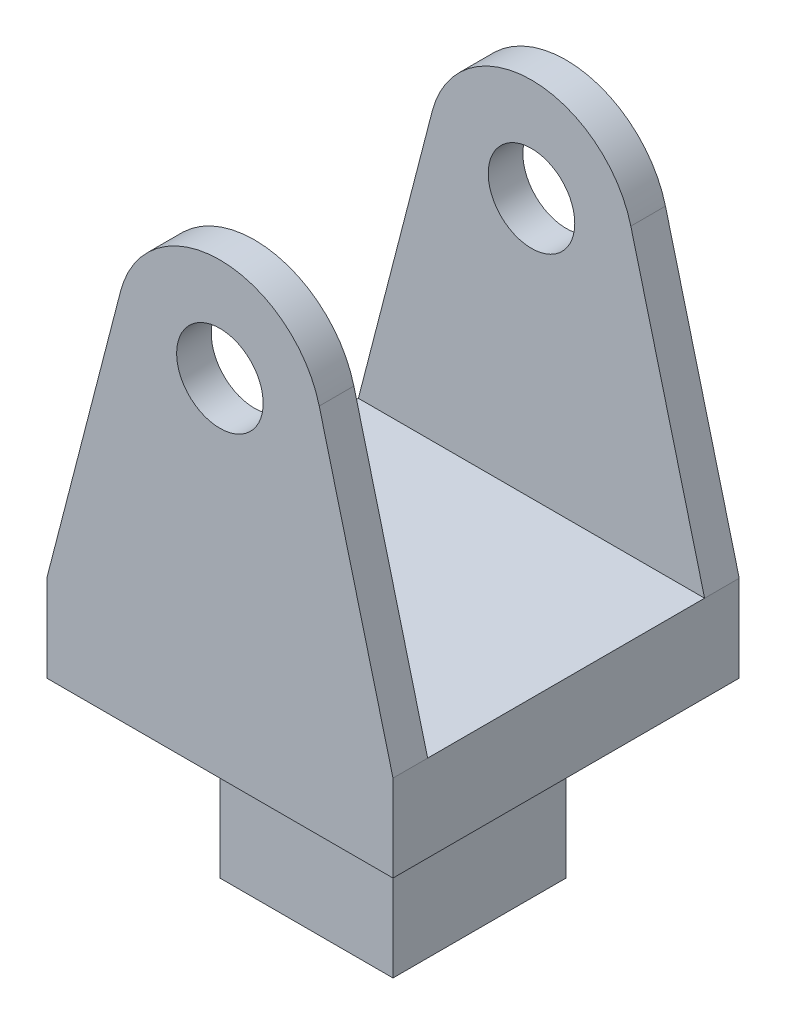
SolidWorks part; units mm, degrees
ref_plane "Front Plane" through (0, 0, 0) normal (0, 0, 1) x (1, 0, 0)
ref_plane "Top Plane" through (0, 0, 0) normal (0, 1, 0) x (1, 0, 0)
ref_plane "Right Plane" through (0, 0, 0) normal (1, 0, 0) x (0, 0, -1)
sketch "Sketch3" plane through (0, 0, 0) normal (0, 1, 0) x (1, 0, 0)
  line L1 (10, 10) -> (-10, 10)
  line L2 (-10, 10) -> (-10, -10)
  line L3 (-10, -10) -> (10, -10)
  line L4 (10, -10) -> (10, 10)
  circle A0 centre (0, 0) radius 10 construction
  dimension "D1" = 20
extrude "Boss-Extrude1" add sketch "Sketch3" along normal blind 30
sketch "Sketch4" plane through (-10, 0, 0) normal (-1, 0, 0) x (0, 0, 1)
  line L0 (-10, 30) -> (10, 30) construction
  line L1 (-8, 30) -> (8, 30)
  line L2 (-8, 30) -> (-8, 5)
  line L3 (-8, 5) -> (8, 5)
  line L4 (8, 30) -> (8, 5)
  line L5 (-10, 0) -> (10, 0) construction
  line L6 (0, 0) -> (0, 28.0953) construction
  dimension "D1" = 5
  dimension "D2" = 16
extrude "Cut-Extrude1" cut sketch "Sketch4" against normal blind 26
sketch "Sketch7" plane through (0, 0, 0) normal (0, 0, 1) x (1, 0, 0)
  line L0 (-10, 0) -> (10, 0) construction
  circle A0 centre (0, 20) radius 2.5
  dimension "D1" = 20
extrude "Cut-Extrude2" cut sketch "Sketch7" against normal mid plane 33 contours A0
sketch "Sketch8" plane through (0, 0, 10) normal (0, 0, 1) x (1, 0, 0)
  line L0 (-10, 5) -> (-5.7391, 21.4835)
  line L1 (-10, 30) -> (-10, 0) construction
  line L2 (-10, 0) -> (10, 0) construction
  line L3 (0, 20) -> (0, 5.8932) construction
  line L4 (10, 5) -> (5.7391, 21.4835)
  line L5 (-10, 5) -> (-10, 30)
  line L6 (-10, 30) -> (10, 30)
  line L7 (10, 30) -> (10, 5)
  arc A0 (5.7391, 21.4835) -> (-5.7391, 21.4835) centre (0, 20) ccw
  dimension "D1" = 5
extrude "Cut-Extrude3" cut sketch "Sketch8" against normal blind 33
sketch "Sketch9" plane through (0, 0, 0) normal (0, -1, 0) x (1, 0, 0)
  line L1 (5, 5) -> (-5, 5)
  line L2 (-5, 5) -> (-5, -5)
  line L3 (-5, -5) -> (5, -5)
  line L4 (5, -5) -> (5, 5)
  circle A0 centre (0, 0) radius 5 construction
extrude "Boss-Extrude2" add sketch "Sketch9" along normal blind 10
